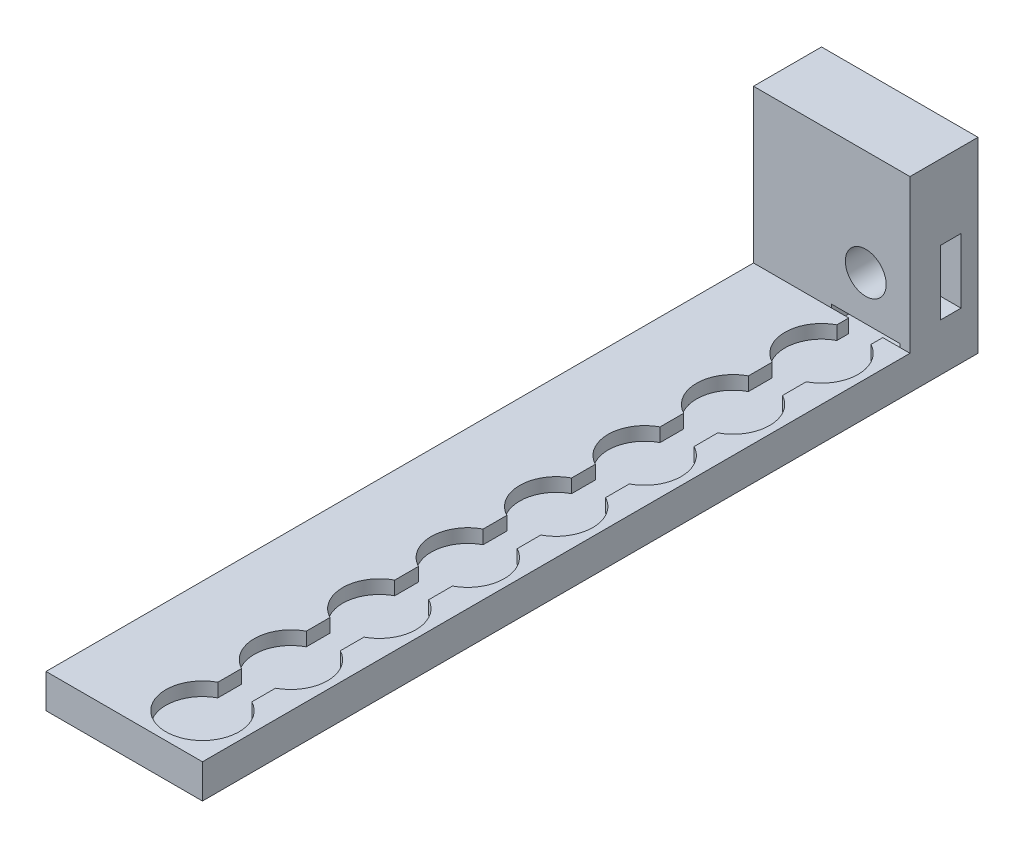
SolidWorks part; units mm, degrees
material "ABS"
ref_plane "Front Plane" through (0, 0, 0) normal (0, 0, 1) x (1, 0, 0)
ref_plane "Top Plane" through (0, 0, 0) normal (0, 1, 0) x (1, 0, 0)
ref_plane "Right Plane" through (0, 0, 0) normal (1, 0, 0) x (0, 0, -1)
sketch "Sketch4" plane through (0, 0, 0) normal (0, 1, 0) x (1, 0, 0)
  circle A0 centre (0, 0) radius 10.75
  dimension "D1" = 21.5
sketch "Sketch5" plane through (0, 0, 0) normal (0, 1, 0) x (1, 0, 0)
  line L1 (-13, 13) -> (13, 13)
  line L2 (-13, 13) -> (-13, -13)
  line L3 (-13, -13) -> (13, -13)
  line L4 (13, 13) -> (13, -13)
  dimension "D1" = 13
  dimension "D2" = 13
  dimension "D3" = 26
  dimension "D4" = 26
extrude "Boss-Extrude1" add sketch "Sketch5" against normal blind 10
extrude "Cut-Extrude1" cut sketch "Sketch4" against normal blind 4 contours A0
sketch "Sketch6" plane through (0, 0, 0) normal (0, 1, 0) x (1, 0, 0)
  line L0 (13, 13) -> (-13, 13) construction
  line L1 (-5, 13) -> (5, 13)
  line L2 (-5, 13) -> (-5, 9.5164)
  line L3 (-5, 9.5164) -> (5, 9.5164)
  line L4 (5, 13) -> (5, 9.5164)
  line L5 (-13, 13) -> (-13, -13) construction
  circle A0 centre (0, 0) radius 10.75 construction
  dimension "D1" = 10
  dimension "D2" = 8
extrude "Cut-Extrude2" cut sketch "Sketch6" against normal blind 4 contours L2 L3 L4 L1
pattern_linear "LPattern1" count 8 spacing 26 along (0, 0, -1) of "Boss-Extrude1", "Cut-Extrude1", "Cut-Extrude2"
sketch "Sketch7" plane through (0, 0, -13) normal (0, 0, 1) x (1, 0, 0)
  line L0 (-5, -4) -> (5, -4) construction
  line L1 (-5, 0) -> (5, 0)
  line L2 (-5, 0) -> (-5, -4)
  line L3 (-5, -4) -> (5, -4)
  line L4 (5, 0) -> (5, -4)
extrude "Cut-Extrude3" cut sketch "Sketch7" against normal through all
sketch "Sketch8" plane through (-13, 0, 0) normal (-1, 0, 0) x (0, 0, 1)
  line L1 (-195, -10) -> (13, -10)
  line L2 (-195, -10) -> (-195, 0)
  line L3 (-195, 0) -> (13, 0)
  line L4 (13, -10) -> (13, 0)
extrude "Boss-Extrude2" add sketch "Sketch8" along normal blind 20
sketch "Sketch9" plane through (0, 0, -195) normal (0, 0, -1) x (-1, 0, 0)
  line L1 (33, -10) -> (-13, -10)
  line L2 (33, -10) -> (33, 0)
  line L3 (33, 0) -> (-13, 0)
  line L4 (-13, -10) -> (-13, 0)
extrude "Boss-Extrude3" add sketch "Sketch9" along normal blind 20
sketch "Sketch10" plane through (0, 0, 0) normal (0, 1, 0) x (1, 0, 0)
  line L0 (13, -13) -> (13, 215) construction
  line L1 (-33, 215) -> (13, 215)
  line L2 (-33, 215) -> (-33, 195)
  line L3 (-33, 195) -> (13, 195)
  line L4 (13, 215) -> (13, 195)
  line L5 (-5, 195) -> (5, 195) construction
  dimension "D1" = 0
extrude "Boss-Extrude4" add sketch "Sketch10" along normal blind 45
sketch "Sketch13" plane through (0, 0, -215) normal (0, 0, -1) x (-1, 0, 0)
  line L0 (-13, -10) -> (33, -10) construction
  line L1 (10, -4) -> (-10, -4)
  line L2 (10, -4) -> (10, 1)
  line L3 (10, 1) -> (-10, 1)
  line L4 (-10, -4) -> (-10, 1)
  line L5 (33, -10) -> (33, 45) construction
  dimension "D1" = 20
  dimension "D2" = 5
  dimension "D3" = 6
  dimension "D4" = 23
extrude "Cut-Extrude4" cut sketch "Sketch13" against normal blind 20
sketch "Sketch14" plane through (0, 0, -215) normal (0, 0, -1) x (-1, 0, 0)
  line L0 (10, 1) -> (-10, 1) construction
  circle A0 centre (0, 14) radius 6
  point P2 (0, 0)
  dimension "D1" = 12
  dimension "D2" = 13
extrude "Cut-Extrude5" cut sketch "Sketch14" against normal blind 45
sketch "Sketch15" plane through (13, 0, 0) normal (1, 0, 0) x (0, 0, -1)
  line L0 (195, 45) -> (195, 0) construction
  line L1 (210, 4) -> (204, 4)
  line L2 (210, 4) -> (210, 23)
  line L3 (210, 23) -> (204, 23)
  line L4 (204, 4) -> (204, 23)
  line L5 (-13, -10) -> (215, -10) construction
  dimension "D1" = 6
  dimension "D2" = 19
  dimension "D3" = 9
  dimension "D4" = 14
extrude "Cut-Extrude6" cut sketch "Sketch15" against normal blind 20
